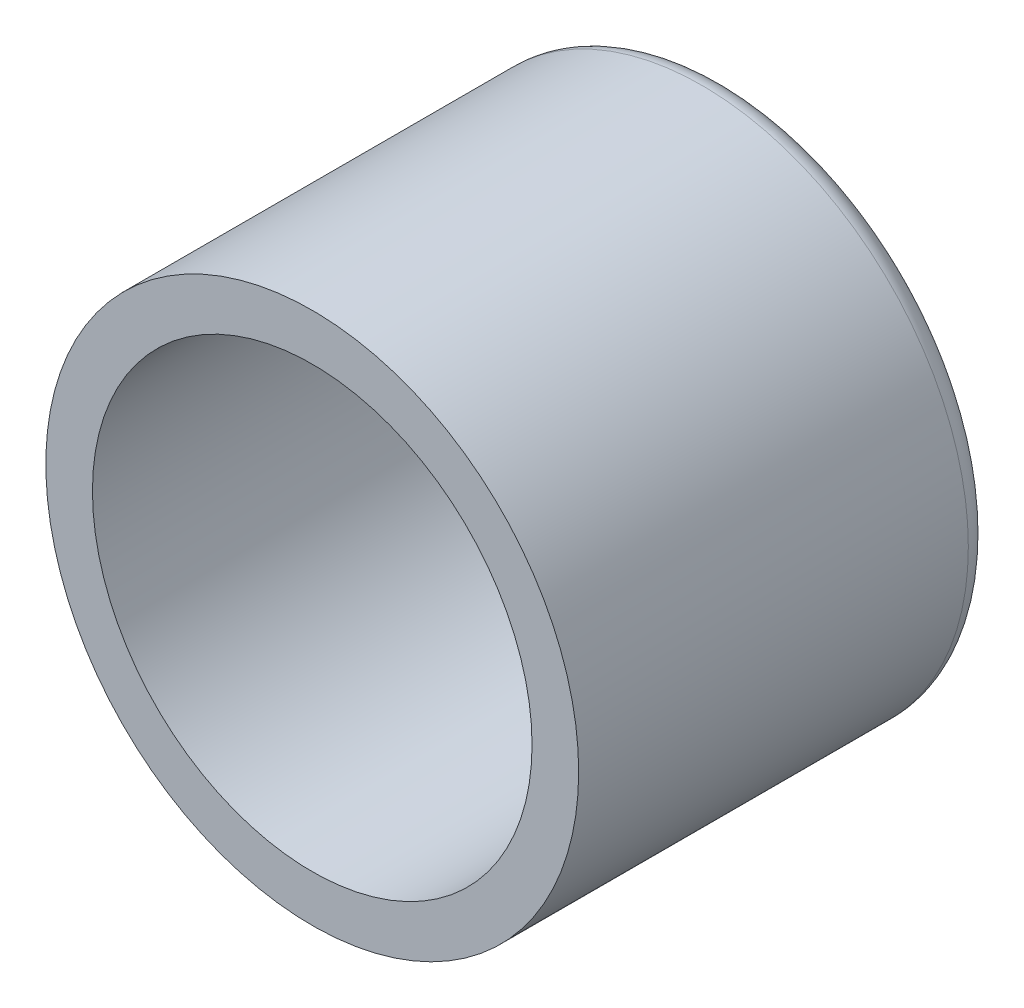
SolidWorks part; units mm, degrees
ref_plane "Alzado" through (0, 0, 0) normal (0, 0, 1) x (1, 0, 0)
ref_plane "Planta" through (0, 0, 0) normal (0, 1, 0) x (1, 0, 0)
ref_plane "Vista lateral" through (0, 0, 0) normal (1, 0, 0) x (0, 0, -1)
sketch "Croquis1" plane through (0, 0, 0) normal (0, 0, 1) x (1, 0, 0)
  circle A0 centre (0, 0) radius 8
  circle A1 centre (0, 0) radius 6.6
extrude "Saliente-Extruir1" add sketch "Croquis1" along normal blind 12.4
fillet "Redondeo1" radius 0.7 1 edges at (8, 0, 0)
